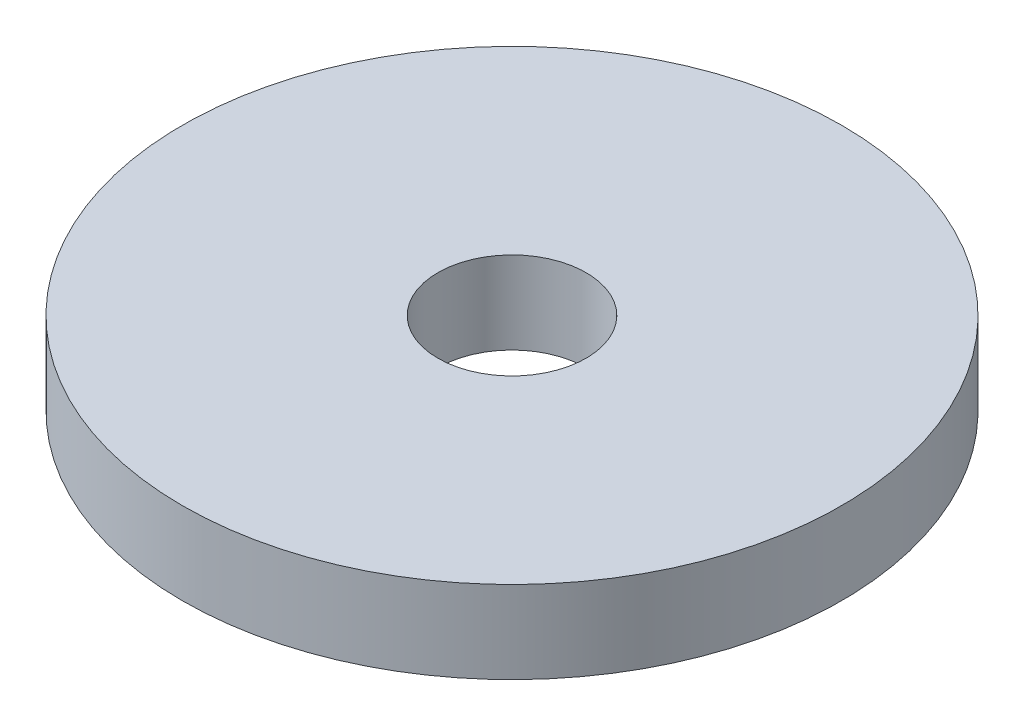
SolidWorks part; units mm, degrees
ref_plane "Front Plane" through (0, 0, 0) normal (0, 0, 1) x (1, 0, 0)
ref_plane "Top Plane" through (0, 0, 0) normal (0, 1, 0) x (1, 0, 0)
ref_plane "Right Plane" through (0, 0, 0) normal (1, 0, 0) x (0, 0, -1)
sketch "Sketch1" plane through (0, 0, 0) normal (0, 1, 0) x (1, 0, 0)
  circle A0 centre (0, 0) radius 20
  circle A1 centre (0, 0) radius 4.5
  dimension "D1" = 40
  dimension "D2" = 9
extrude "Boss-Extrude1" add sketch "Sketch1" along normal blind 5
